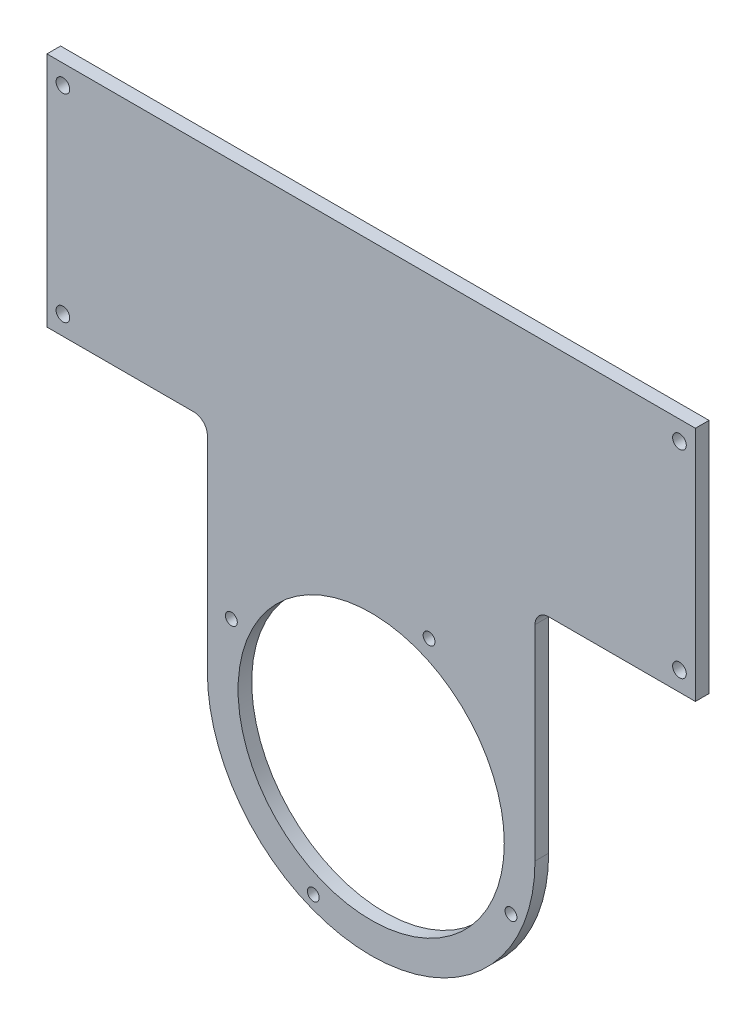
SolidWorks part; units mm, degrees
ref_plane "Front Plane" through (0, 0, 0) normal (0, 0, 1) x (1, 0, 0)
ref_plane "Top Plane" through (0, 0, 0) normal (0, 1, 0) x (1, 0, 0)
ref_plane "Right Plane" through (0, 0, 0) normal (1, 0, 0) x (0, 0, -1)
sketch "Sketch1" plane through (0, 0, 0) normal (0, 0, 1) x (1, 0, 0)
  line L0 (-36, 0) -> (-36, 48)
  line L1 (-71.25, 100) -> (71.25, 100)
  line L2 (-71.25, 100) -> (-71.25, 48)
  line L3 (-71.25, 48) -> (-36, 48)
  line L4 (71.25, 100) -> (71.25, 48)
  line L5 (-71.25, 100) -> (71.25, 48) construction
  line L6 (-71.25, 48) -> (71.25, 100) construction
  line L7 (67.75, 52.25) -> (-67.75, 52.25) construction
  line L8 (67.75, 52.25) -> (67.75, 95.75) construction
  line L9 (67.75, 95.75) -> (-67.75, 95.75) construction
  line L10 (-67.75, 52.25) -> (-67.75, 95.75) construction
  line L11 (67.75, 52.25) -> (-67.75, 95.75) construction
  line L12 (67.75, 95.75) -> (-67.75, 52.25) construction
  line L13 (36, 0) -> (36, 48)
  line L14 (36, 48) -> (71.25, 48)
  arc A0 (-36, 0) -> (36, 0) centre (0, 0) ccw
  circle A1 centre (-67.75, 95.75) radius 1.5
  circle A2 centre (67.75, 95.75) radius 1.5
  circle A3 centre (67.75, 52.25) radius 1.5
  circle A4 centre (-67.75, 52.25) radius 1.5
  point P0 (0, 74)
  point P9 (0, 74)
  dimension "D3" = 72
  dimension "D7" = 3
  dimension "D1" = 142.5
  dimension "D2" = 52
  dimension "D4" = 48
  dimension "D5" = 135.5
  dimension "D6" = 43.5
extrude "Boss-Extrude1" add sketch "Sketch1" along normal blind 3
fillet "Fillet1" radius 3 2 edges at (36, 48, 1.5) (-36, 48, 1.5)
sketch "Sketch2" plane through (0, 0, 3) normal (0, 0, 1) x (1, 0, 0)
  line L0 (0, 0) -> (0, 33.25) construction
  circle A0 centre (0, 0) radius 29.25
  circle A1 centre (0, 0) radius 33.25 construction
  circle A2 centre (12.7242, 30.719) radius 1.3
  circle A3 centre (30.719, -12.7242) radius 1.3
  circle A4 centre (-12.7242, -30.719) radius 1.3
  circle A5 centre (-30.719, 12.7242) radius 1.3
  point P6 (0, 0)
  point P8 (0, 0)
  point P16 (0, 0)
  dimension "D1" = 58.5
  dimension "D2" = 66.5
  dimension "D4" = 2.6
  dimension "D3" = 22.5
  dimension "D5" = 4
extrude "Cut-Extrude1" cut sketch "Sketch2" against normal blind 3
